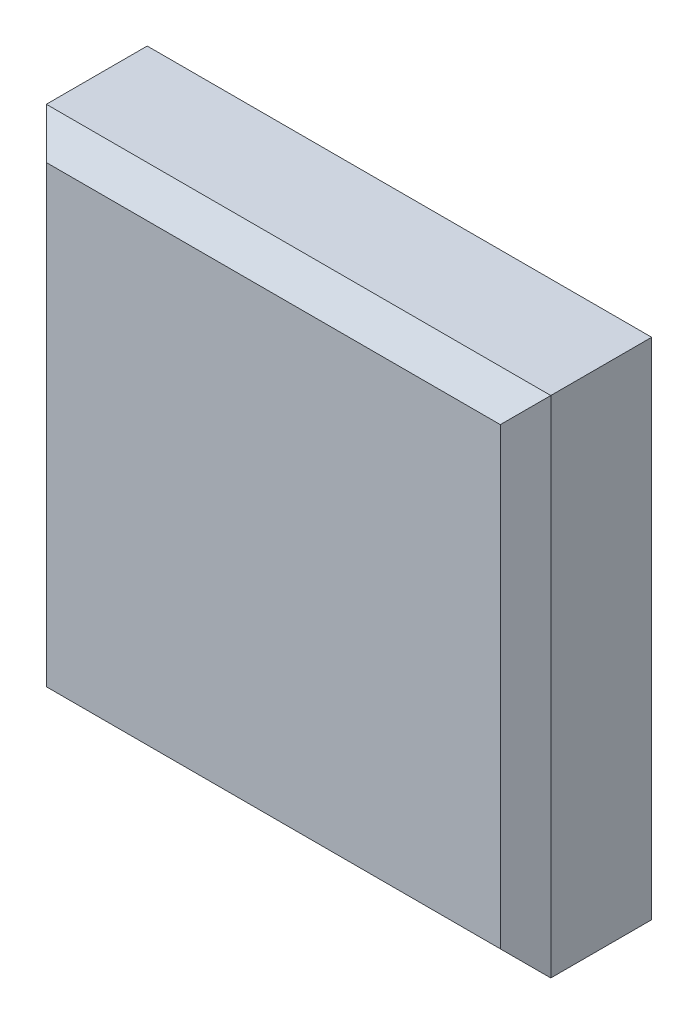
SolidWorks part; units mm, degrees
ref_plane "Plan de face" through (0, 0, 0) normal (0, 0, 1) x (1, 0, 0)
ref_plane "Plan de dessus" through (0, 0, 0) normal (0, 1, 0) x (1, 0, 0)
ref_plane "Plan de droite" through (0, 0, 0) normal (1, 0, 0) x (0, 0, -1)
sketch "Esquisse1" plane through (0, 0, 0) normal (0, 0, 1) x (1, 0, 0)
  line L1 (0, 0) -> (20, 0)
  line L2 (0, 0) -> (0, -20)
  line L3 (0, -20) -> (20, -20)
  line L4 (20, 0) -> (20, -20)
  dimension "D1" = 20
  dimension "D2" = 20
extrude "Boss.-Extru.1" add sketch "Esquisse1" along normal blind 5
chamfer "Chanfrein1" distance 1 angle 45 4 edges at (10, 0, 5) (20, -10, 5) (10, -20, 5) (0, -10, 5)
